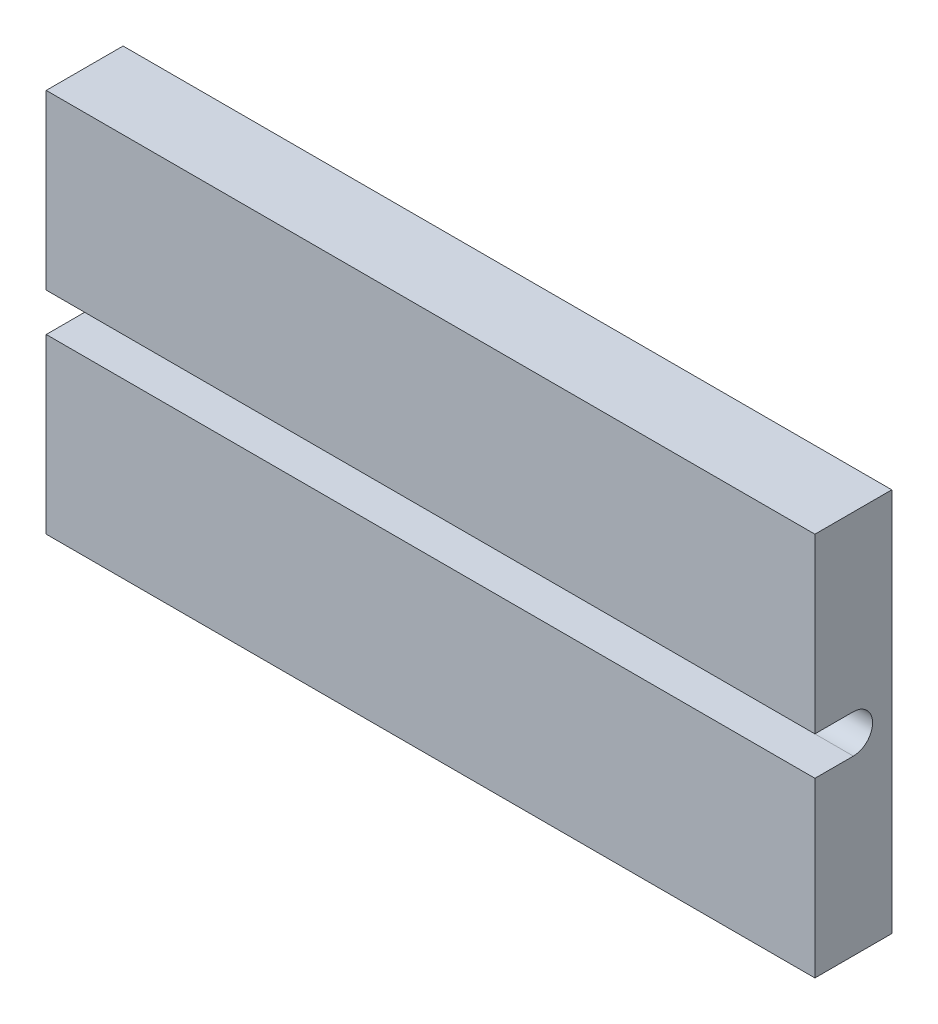
SolidWorks part; units mm, degrees
ref_plane "前视基准面" through (0, 0, 0) normal (0, 0, 1) x (1, 0, 0)
ref_plane "上视基准面" through (0, 0, 0) normal (0, 1, 0) x (1, 0, 0)
ref_plane "右视基准面" through (0, 0, 0) normal (1, 0, 0) x (0, 0, -1)
other "Configuration Table"
sketch "草图1" plane through (0, 0, 0) normal (0, 0, 1) x (1, 0, 0)
  line L1 (-100, -50) -> (100, -50)
  line L2 (-100, -50) -> (-100, 50)
  line L3 (-100, 50) -> (100, 50)
  line L4 (100, -50) -> (100, 50)
  line L5 (-100, -50) -> (100, 50) construction
  line L6 (-100, 50) -> (100, -50) construction
  point P0 (0, 0)
  dimension "D1" = 200
  dimension "D2" = 100
extrude "凸台-拉伸1" add sketch "草图1" along normal blind 20
sketch "草图2" plane through (-100, 0, 0) normal (-1, 0, 0) x (0, 0, 1)
  line L1 (10, -5) -> (20, -5)
  line L2 (20, 50) -> (20, -50) construction
  line L3 (20, -5) -> (20, 5)
  line L4 (20, 5) -> (10, 5)
  line L6 (20, 50) -> (0, 50) construction
  line L7 (20, -50) -> (0, -50) construction
  arc A1 (10, 5) -> (10, -5) centre (10, 0) ccw
  point P2 (0, 0)
  point P6 (3.6892, 50)
  dimension "D1" = 10
  dimension "D2" = 45
  dimension "D4" = 5
  dimension "D3" = 50
  dimension "D5" = 10
extrude "切除-拉伸1" cut sketch "草图2" against normal through all
